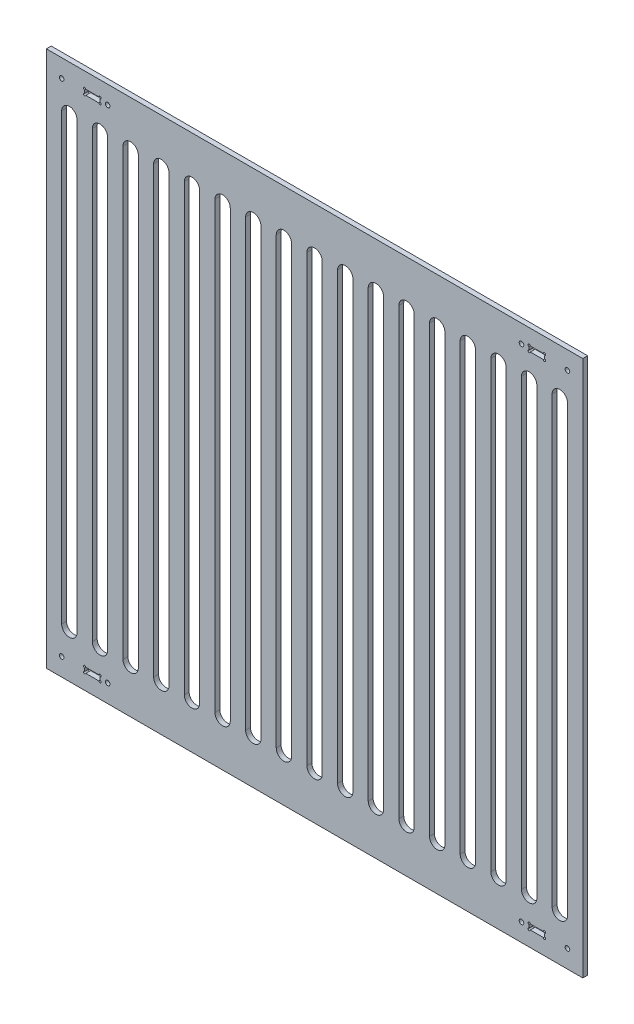
SolidWorks part; units mm, degrees
ref_plane "Front Plane" through (0, 0, 0) normal (0, 0, 1) x (1, 0, 0)
ref_plane "Top Plane" through (0, 0, 0) normal (0, 1, 0) x (1, 0, 0)
ref_plane "Right Plane" through (0, 0, 0) normal (1, 0, 0) x (0, 0, -1)
sketch "Sketch1" plane through (0, 0, 0) normal (0, 0, 1) x (1, 0, 0)
  line L5 (350, -350) -> (-350, -350)
  line L6 (350, -350) -> (350, 350)
  line L7 (350, 350) -> (-350, 350)
  line L8 (-350, -350) -> (-350, 350)
  line L9 (350, -350) -> (-350, 350) construction
  line L10 (350, 350) -> (-350, -350) construction
  point P0 (0, 0)
  dimension "D1" = 700
  dimension "D2" = 700
extrude "Boss-Extrude1" add sketch "Sketch1" along normal blind 6.35
sketch "Sketch2" plane through (0, 0, 6.35) normal (0, 0, 1) x (1, 0, 0)
  line L0 (-350, 350) -> (-350, -350) construction
  line L1 (-300, 330) -> (-280, 330)
  line L2 (-300, 330) -> (-300, 323.142)
  line L3 (-300, 323.142) -> (-280, 323.142)
  line L4 (-280, 330) -> (-280, 323.142)
  line L5 (350, 350) -> (-350, 350) construction
  circle A0 centre (-300, 330) radius 1.5
  circle A1 centre (-280, 330) radius 1.5
  circle A2 centre (-300, 323.142) radius 1.5
  circle A3 centre (-280, 323.142) radius 1.5
  circle A4 centre (-330, 326.57) radius 3
  circle A5 centre (-270, 326.57) radius 3
  dimension "D5" = 20
  dimension "D7" = 80
  dimension "D1" = 6.858
  dimension "D2" = 20
  dimension "D3" = 50
  dimension "D4" = 20
  dimension "D6" = 23.43
extrude "Cut-Extrude1" cut sketch "Sketch2" against normal through all contours A3 L4 A1 L1 A0 L2 A2 L3 | L2 A0 L1 | L1 A0 L2 | L2 A2 L3 | L3 A2 L2 | L1 A1 L4 | L4 A1 L1 | L4 A3 L3 | L3 A3 L4 | A4 | A5
mirror "Mirror1" about plane through (0, 0, 0) normal (0, 1, 0) of "Cut-Extrude1"
mirror "Mirror2" about plane through (0, 0, 0) normal (1, 0, 0) of "Mirror1", "Cut-Extrude1"
sketch "Sketch3" plane through (0, 0, 6.35) normal (0, 0, 1) x (1, 0, 0)
  line L0 (0, 290) -> (0, -290) construction
  line L1 (10, 290) -> (10, -290)
  line L2 (-10, 290) -> (-10, -290)
  line L4 (350, 350) -> (-350, 350) construction
  line L5 (-350, -350) -> (350, -350) construction
  arc A0 (10, 290) -> (-10, 290) centre (0, 290) ccw
  arc A1 (-10, -290) -> (10, -290) centre (0, -290) ccw
  point P3 (0, 0)
  dimension "D1" = 60
  dimension "D2" = 60
extrude "Cut-Extrude2" cut sketch "Sketch3" against normal through all
pattern_linear "LPattern1" count 9 spacing 40 along (1, 0, 0) of "Cut-Extrude2"
mirror "Mirror3" about plane through (0, 0, 0) normal (1, 0, 0) of "LPattern1"
